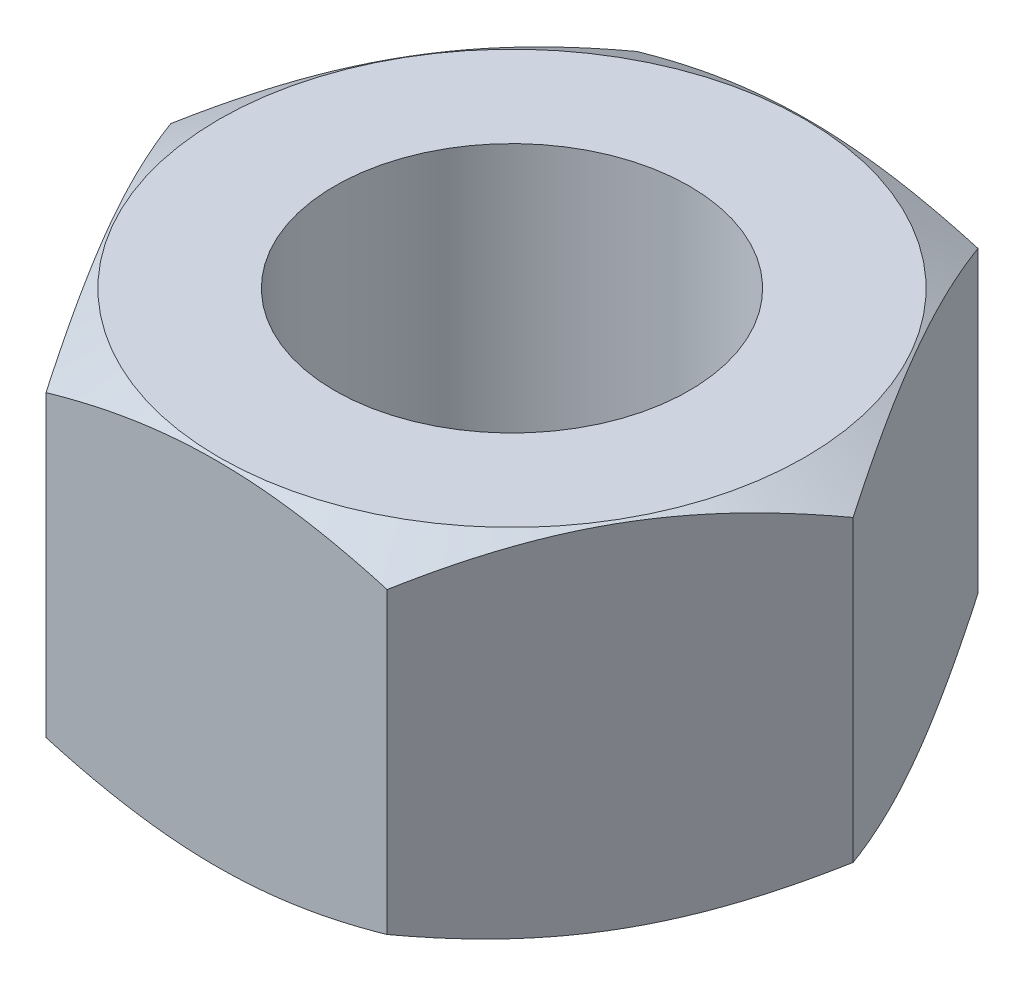
SolidWorks part; units mm, degrees
ref_plane "Front Plane" through (0, 0, 0) normal (0, 0, 1) x (1, 0, 0)
ref_plane "Top Plane" through (0, 0, 0) normal (0, 1, 0) x (1, 0, 0)
ref_plane "Right Plane" through (0, 0, 0) normal (1, 0, 0) x (0, 0, -1)
sketch "Sketch1" plane through (0, 0, 0) normal (0, 1, 0) x (1, 0, 0)
  line L1 (8.6603, 0) -> (4.3301, 7.5)
  line L2 (4.3301, 7.5) -> (-4.3301, 7.5)
  line L3 (-4.3301, 7.5) -> (-8.6603, 0)
  line L4 (-8.6603, 0) -> (-4.3301, -7.5)
  line L5 (-4.3301, -7.5) -> (4.3301, -7.5)
  line L6 (4.3301, -7.5) -> (8.6603, 0)
  circle A0 centre (0, 0) radius 7.5 construction
  circle A1 centre (0, 0) radius 4.5
  dimension "D1" = 9
  dimension "D2" = 15
extrude "Boss-Extrude1" add sketch "Sketch1" along normal mid plane 9
sketch "Sketch3" plane through (0, 0, 0) normal (1, 0, 0) x (0, 0, -1)
  line L0 (-1.3433, 0) -> (49998.6567, 0) construction
  line L1 (4.2156, 6.3582) -> (9.4175, 3.3549)
  line L2 (9.4175, 3.3549) -> (9.4175, 6.3582)
  line L3 (9.4175, 6.3582) -> (4.2156, 6.3582)
  line L4 (0, 0) -> (0, 50000) construction
  line L5 (9.4175, -6.3582) -> (4.2156, -6.3582)
  line L6 (9.4175, -3.3549) -> (9.4175, -6.3582)
  line L7 (4.2156, -6.3582) -> (9.4175, -3.3549)
  dimension "D1" = 30
revolve "Cut-Revolve2" cut sketch "Sketch3" angle 360 about L4
sketch "Sketch2" plane through (0, 0, 0) normal (0, 0, 1) x (1, 0, 0)
  line L0 (0, 0) -> (50000, 0) construction
  line L2 (4.549, 6.3582) -> (10.7608, 2.7719)
  line L3 (10.7608, 2.7719) -> (10.7608, 6.3582)
  line L4 (10.7608, 6.3582) -> (4.549, 6.3582)
  line L5 (0, 0) -> (0, 50000) construction
  line L6 (10.7608, -6.3582) -> (4.549, -6.3582)
  line L7 (10.7608, -2.7719) -> (10.7608, -6.3582)
  line L8 (4.549, -6.3582) -> (10.7608, -2.7719)
  dimension "D1" = 30
revolve "Cut-Revolve1" cut sketch "Sketch2" angle 360 about L5
